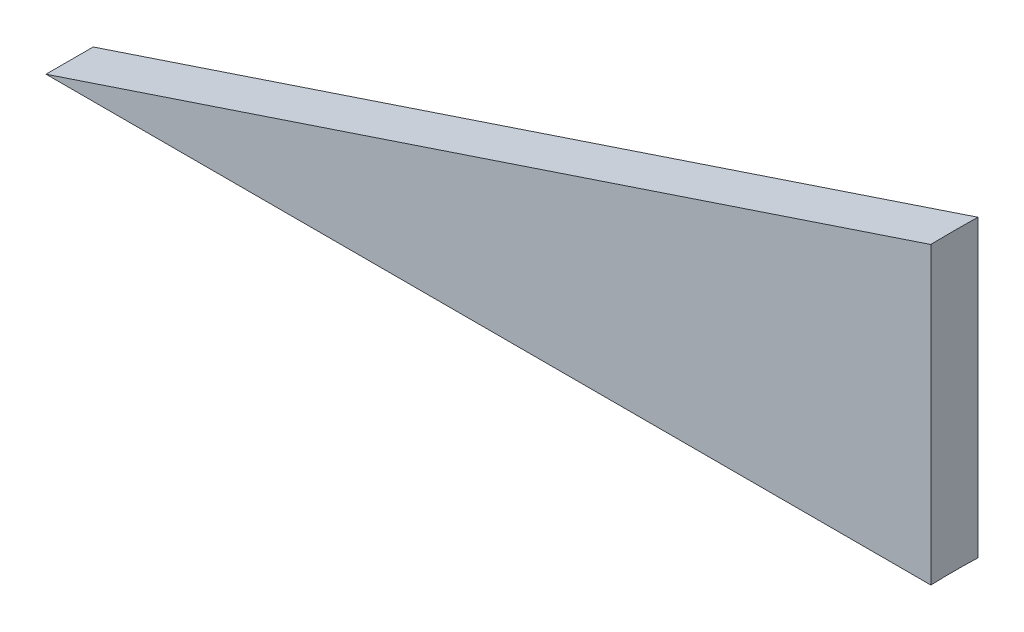
SolidWorks part; units mm, degrees
ref_plane "Front Plane" through (0, 0, 0) normal (0, 0, 1) x (1, 0, 0)
ref_plane "Top Plane" through (0, 0, 0) normal (0, 1, 0) x (1, 0, 0)
ref_plane "Right Plane" through (0, 0, 0) normal (1, 0, 0) x (0, 0, -1)
sketch "Sketch1" plane through (0, 0, 0) normal (0, 0, 1) x (1, 0, 0)
  line L0 (0, 0) -> (150, 0)
  line L1 (150, 0) -> (150, 50)
  line L2 (150, 50) -> (0, 0)
  dimension "D1" = 150
  dimension "D2" = 50
extrude "Boss-Extrude1" add sketch "Sketch1" along normal blind 8
sketch "Sketch2" plane through (0, 0, 0) normal (0, -1, 0) x (1, 0, 0)
  line L0 (0, 8) -> (0, 0) construction
  circle A0 centre (274.936, 4) radius 125
  point P2 (0, 4)
  dimension "D1" = 250
extrude "Cut-Extrude1" cut sketch "Sketch2" against normal through all
